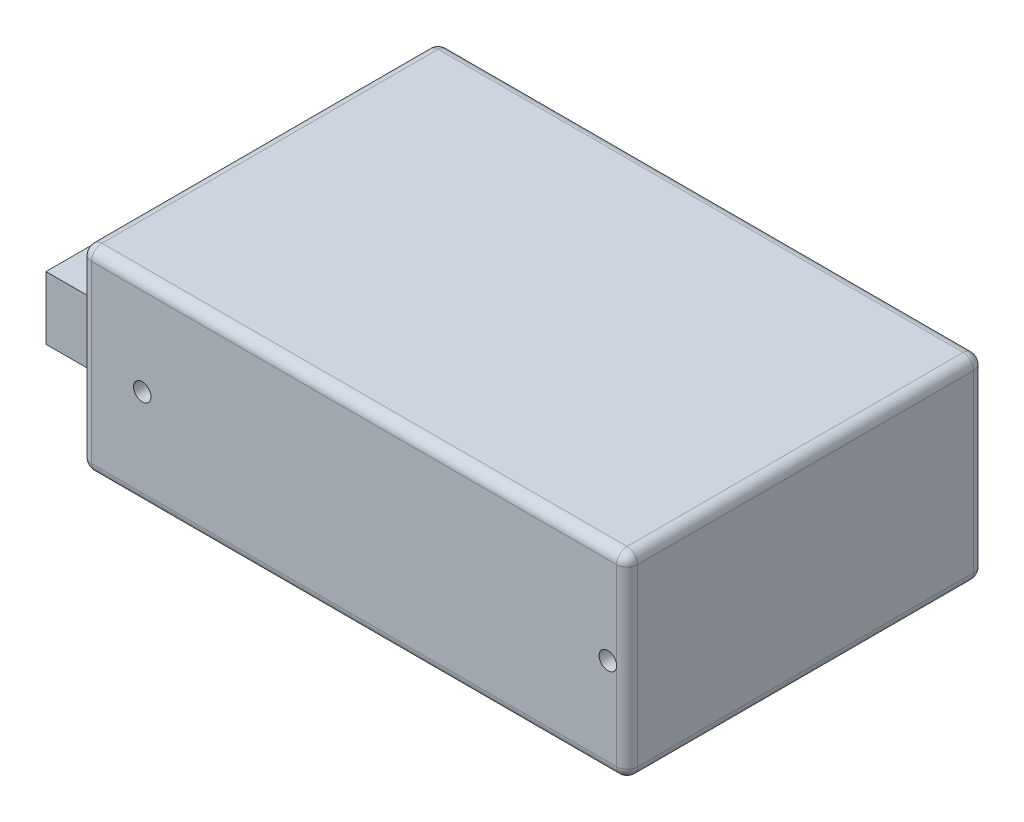
SolidWorks part; units mm, degrees
ref_plane "Front Plane" through (0, 0, 0) normal (0, 0, 1) x (1, 0, 0)
ref_plane "Top Plane" through (0, 0, 0) normal (0, 1, 0) x (1, 0, 0)
ref_plane "Right Plane" through (0, 0, 0) normal (1, 0, 0) x (0, 0, -1)
sketch "Sketch2" plane through (0, 0, 0) normal (0, 1, 0) x (1, 0, 0)
  line L1 (-39, -25.5) -> (39, -25.5)
  line L2 (-39, -25.5) -> (-39, 25.5)
  line L3 (-39, 25.5) -> (39, 25.5)
  line L4 (39, -25.5) -> (39, 25.5)
  line L5 (-39, -25.5) -> (39, 25.5) construction
  line L6 (-39, 25.5) -> (39, -25.5) construction
  point P0 (0, 0)
  dimension "D1" = 78
  dimension "D2" = 51
extrude "Boss-Extrude1" add sketch "Sketch2" along normal blind 28
sketch "Sketch3" plane through (-39, 0, 0) normal (-1, 0, 0) x (0, 0, 1)
  line L0 (-25.5, 28) -> (-25.5, 0) construction
  line L1 (-23.5, 4) -> (16.5, 4)
  line L2 (-23.5, 4) -> (-23.5, 13)
  line L3 (-23.5, 13) -> (16.5, 13)
  line L4 (16.5, 4) -> (16.5, 13)
  line L5 (-23.5, 4) -> (16.5, 13) construction
  line L6 (-23.5, 13) -> (16.5, 4) construction
  line L7 (-25.5, 0) -> (25.5, 0) construction
  point P0 (-3.5, 8.5)
  dimension "D1" = 40
  dimension "D2" = 9
  dimension "D3" = 2
  dimension "D4" = 4
extrude "Boss-Extrude2" add sketch "Sketch3" along normal blind 14 separate body
hole_wizard "Tap Drill for M3 Tap1" positions "3DSketch2" profile "Sketch5" hole size "M3" standard "ISO"
sketch3d "3DSketch2"
  line L0 (39, 0, 25.5) -> (39, 0, -25.5) construction
  line L2 (39, 28, 25.5) -> (39, 0, 25.5) construction
  line L3 (-39, 0, 25.5) -> (39, 0, 25.5) construction
  point P0 (-26.5, 0, 0.1)
  point P2 (28.5, 0, 0.1)
  point P4 (-30.25, 14, 25.5)
  point P6 (36.25, 14, 25.5)
  point P17 (60.4119, -28.3746, 0)
  dimension "D1" = 10.5
  dimension "D2" = 65.5
  dimension "D3" = 25.4
  dimension "D4" = 25.4
  dimension "D5" = 2.75
  dimension "D6" = 69.25
  dimension "D7" = 14
  dimension "D8" = 14
sketch "Sketch5" plane through (-26.5, 0, 0.1) normal (1, 0, 0) x (0, 0, -1)
  line L0 (0, 0) -> (0, 7.7511)
  line L1 (0, 7.7511) -> (1.25, 7)
  line L2 (1.25, 7) -> (1.25, 0)
  line L5 (1.25, 0) -> (0, 0)
  line L10 (0, 7.7511) -> (-1.25, 7) construction
  line L11 (0, -6.35) -> (0, 107.95) construction
  dimension "Hole Dia." = 2.5
  dimension "Hole Depth" = 7
  dimension "Drill Angle" = 118
fillet "Fillet1" radius 1.5 12 edges at (-39, 14, -25.5) (-39, 14, 25.5) (39, 14, 25.5) (39, 14, -25.5) (0, 0, -25.5) (-39, 0, 0) (0, 0, 25.5) (39, 0, 0) (0, 28, 25.5) (-39, 28, 0) (0, 28, -25.5) (39, 28, 0)
